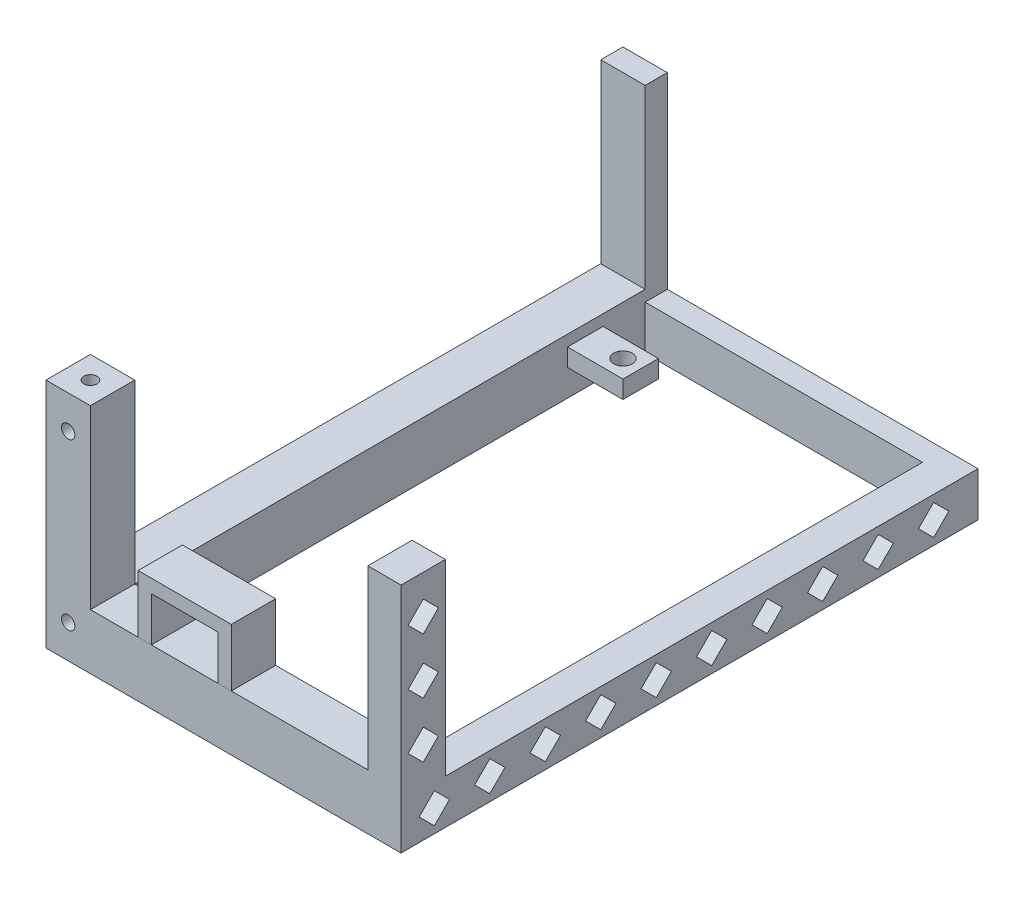
SolidWorks part; units mm, degrees
ref_plane "Front Plane" through (0, 0, 0) normal (0, 0, 1) x (1, 0, 0)
ref_plane "Top Plane" through (0, 0, 0) normal (0, 1, 0) x (1, 0, 0)
ref_plane "Right Plane" through (0, 0, 0) normal (1, 0, 0) x (0, 0, -1)
sketch "Sketch1" plane through (0, 0, 0) normal (0, 1, 0) x (1, 0, 0)
  line L0 (0, 0) -> (-45, 0) construction
  line L1 (35, -65) -> (-45, -65)
  line L2 (35, -65) -> (35, 65)
  line L3 (35, 65) -> (-45, 65)
  line L4 (-45, -65) -> (-45, 65)
  line L5 (0, 0) -> (35, 0) construction
  point P0 (0, 0)
  dimension "D1" = 65
  dimension "D2" = 65
extrude "Boss-Extrude1" add sketch "Sketch1" along normal blind 10
sketch "Sketch2" plane through (0, 10, 0) normal (0, 1, 0) x (1, 0, 0)
  line L0 (35, -65) -> (-45, -65)
  line L1 (-45, -65) -> (-45, 65)
  line L2 (-45, 65) -> (-35, 65)
  line L3 (35, 65) -> (-45, 65) construction
  line L4 (35, -65) -> (35, -55)
  line L5 (35, -65) -> (35, 65) construction
  line L6 (-35, 65) -> (-35, -55)
  line L7 (-35, -55) -> (35, -55)
extrude "Boss-Extrude2" add sketch "Sketch2" along normal blind 42.3
sketch "Sketch3" plane through (35, 0, 0) normal (1, 0, 0) x (0, 0, -1)
  line L1 (20.925, 5) -> (17.5, 8.425)
  line L39 (-55, 10) -> (-65, 10) construction
  line L40 (17.5, 8.425) -> (14.075, 5)
  line L41 (14.075, 5) -> (17.5, 1.575)
  line L42 (17.5, 1.575) -> (20.925, 5)
  line L56 (-65, 52.3) -> (-65, 0) construction
  line L57 (33.425, 5) -> (30, 8.425)
  line L58 (-55, 10) -> (-55, 0) construction
  line L73 (-65, 0) -> (65, 0) construction
  line L74 (30, 8.425) -> (26.575, 5)
  line L75 (-55, 5) -> (65, 5) construction
  line L76 (26.575, 5) -> (30, 1.575)
  line L77 (65, 10) -> (65, 0) construction
  line L118 (5, 8.425) -> (5, 1.575) construction
  line L119 (5, 8.425) -> (1.575, 5)
  line L120 (1.575, 5) -> (5, 1.575)
  line L121 (5, 1.575) -> (8.425, 5)
  line L122 (8.425, 5) -> (5, 8.425)
  line L139 (-4.075, 5) -> (-7.5, 8.425)
  line L140 (-7.5, 8.425) -> (-10.925, 5)
  line L141 (-10.925, 5) -> (-7.5, 1.575)
  line L142 (-7.5, 1.575) -> (-4.075, 5)
  line L143 (-16.575, 5) -> (-20, 8.425)
  line L144 (-20, 8.425) -> (-23.425, 5)
  line L145 (-23.425, 5) -> (-20, 1.575)
  line L146 (-20, 1.575) -> (-16.575, 5)
  line L147 (-29.075, 5) -> (-32.5, 8.425)
  line L148 (-32.5, 8.425) -> (-35.925, 5)
  line L149 (-35.925, 5) -> (-32.5, 1.575)
  line L150 (-32.5, 1.575) -> (-29.075, 5)
  line L151 (-41.575, 5) -> (-45, 8.425)
  line L152 (-45, 8.425) -> (-48.425, 5)
  line L153 (-48.425, 5) -> (-45, 1.575)
  line L154 (-45, 1.575) -> (-41.575, 5)
  line L155 (-54.075, 5) -> (-57.5, 8.425)
  line L156 (-57.5, 8.425) -> (-60.925, 5)
  line L157 (-60.925, 5) -> (-57.5, 1.575)
  line L158 (-57.5, 1.575) -> (-54.075, 5)
  line L159 (-60, 10) -> (-60, 52.3) construction
  line L160 (-65, 52.3) -> (-55, 52.3) construction
  line L161 (-63.425, 31.15) -> (-56.575, 31.15) construction
  line L162 (-63.425, 31.15) -> (-60, 34.575)
  line L163 (-60, 34.575) -> (-56.575, 31.15)
  line L164 (-56.575, 31.15) -> (-60, 27.725)
  line L165 (-60, 27.725) -> (-63.425, 31.15)
  line L166 (-60, 40.225) -> (-63.425, 43.65)
  line L167 (-63.425, 43.65) -> (-60, 47.075)
  line L168 (-60, 47.075) -> (-56.575, 43.65)
  line L169 (-56.575, 43.65) -> (-60, 40.225)
  line L170 (-60, 15.225) -> (-63.425, 18.65)
  line L171 (-63.425, 18.65) -> (-60, 22.075)
  line L172 (-60, 22.075) -> (-56.575, 18.65)
  line L173 (-56.575, 18.65) -> (-60, 15.225)
  line L174 (30, 1.575) -> (33.425, 5)
  line L175 (45.925, 5) -> (42.5, 8.425)
  line L176 (42.5, 8.425) -> (39.075, 5)
  line L177 (39.075, 5) -> (42.5, 1.575)
  line L178 (42.5, 1.575) -> (45.925, 5)
  line L179 (58.425, 5) -> (55, 8.425)
  line L180 (55, 8.425) -> (51.575, 5)
  line L181 (51.575, 5) -> (55, 1.575)
  line L182 (55, 1.575) -> (58.425, 5)
  point P15 (5, 5)
  point P61 (-60, 31.15)
  dimension "D1" = 6
  dimension "D2" = 2
  dimension "D3" = 2
extrude "Cut-Extrude1" cut sketch "Sketch3" against normal blind 5.25
sketch "Sketch4" plane through (0, 10, 0) normal (0, 1, 0) x (1, 0, 0)
  line L0 (-35, 65) -> (-26.5, 65) construction
  line L1 (35, 65) -> (-35, 65) construction
  line L2 (-26.5, 65) -> (-26.5, 46.5) construction
  circle A0 centre (-26.5, 46.5) radius 2.1
  dimension "D1" = 4.2
extrude "Cut-Extrude2" cut sketch "Sketch4" against normal through all
sketch "Sketch5" plane through (0, 10, 0) normal (0, 1, 0) x (1, 0, 0)
  line L0 (-35, -55) -> (-35, 42.5)
  line L1 (27.5, 60) -> (-35, 60)
  line L3 (27.5, 60) -> (27.5, -55)
  line L4 (-35, -55) -> (27.5, -55)
  line L6 (35, -55) -> (35, 65) construction
  line L7 (35, -55) -> (-35, -55) construction
  line L8 (-35, 42.5) -> (-22.5, 42.5)
  line L10 (-35, -55) -> (-35, 65) construction
  line L11 (-35, 60) -> (-35, 50.5)
  line L12 (-35, 50.5) -> (-22.5, 50.5)
  line L13 (-22.5, 50.5) -> (-22.5, 42.5)
  circle A0 centre (-26.5, 46.5) radius 2.1 construction
  dimension "D3" = 4
  dimension "D4" = 4
  dimension "D2" = 4
  dimension "D1" = 7.5
extrude "Cut-Extrude3" cut sketch "Sketch5" against normal through all
sketch "Sketch7" plane through (-35, 0, 0) normal (1, 0, 0) x (0, 0, -1)
  line L0 (-55, 52.3) -> (-55, 12.5)
  line L1 (-55, 52.3) -> (-55, 0) construction
  line L2 (-55, 12.5) -> (60, 12.5)
  line L3 (60, 12.5) -> (60, 52.3)
  line L4 (-55, 52.3) -> (65, 52.3) construction
  line L5 (60, 52.3) -> (-55, 52.3)
  line L6 (65, 52.3) -> (65, 10) construction
  line L7 (42.5, 0) -> (-55, 0) construction
  dimension "D1" = 5
  dimension "D2" = 12.5
extrude "Cut-Extrude4" cut sketch "Sketch7" against normal through all
sketch "Sketch8" plane through (0, 0, 55) normal (0, 0, -1) x (-1, 0, 0)
  line L0 (35, 12.5) -> (35, 52.3)
  line L1 (-35, 52.3) -> (45, 52.3) construction
  line L2 (35, 52.3) -> (-27.5, 52.3)
  line L7 (35, 12.5) -> (-27.5, 12.5)
  line L8 (-27.5, 12.5) -> (-27.5, 52.3)
extrude "Cut-Extrude5" cut sketch "Sketch8" against normal blind 10
sketch "Sketch9" plane through (0, 52.3, 0) normal (0, 1, 0) x (1, 0, 0)
  line L0 (-45, -60) -> (-40, -60) construction
  line L1 (-45, -55) -> (-45, -65) construction
  circle A0 centre (-40, -60) radius 1.5
extrude "Cut-Extrude6" cut sketch "Sketch9" against normal blind 4
sketch "Sketch10" plane through (0, 0, 0) normal (0, -1, 0) x (1, 0, 0)
  circle A0 centre (-40, 60) radius 1.5 construction
  circle A1 centre (-40, 60) radius 1.5
extrude "Cut-Extrude7" cut sketch "Sketch10" against normal blind 4
sketch "Sketch11" plane through (0, 0, 0) normal (0, -1, 0) x (1, 0, 0)
  line L0 (-35, -42.5) -> (-22.5, -42.5)
  line L1 (-22.5, -42.5) -> (-22.5, -50.5)
  line L2 (-22.5, -50.5) -> (-35, -50.5)
  line L3 (-35, -50.5) -> (-35, -42.5)
extrude "Cut-Extrude8" cut sketch "Sketch11" against normal blind 6
sketch "Sketch13" plane through (0, 0, 65) normal (0, 0, 1) x (1, 0, 0)
  line L4 (-21.25, 12.5) -> (-6.25, 12.5)
  line L5 (27.5, 12.5) -> (-35, 12.5) construction
  line L15 (-21.25, 12.5) -> (-21.25, 22.5)
  line L16 (-21.25, 22.5) -> (-6.25, 22.5)
  line L17 (-6.25, 22.5) -> (-6.25, 12.5)
  line L20 (-3.25, 12.5) -> (-3.25, 25.5)
  line L21 (-3.25, 25.5) -> (-24.25, 25.5)
  line L22 (-24.25, 25.5) -> (-24.25, 12.5)
  line L23 (-24.25, 12.5) -> (-21.25, 12.5)
  line L24 (-6.25, 12.5) -> (-3.25, 12.5)
  point P8 (-13.75, 12.5)
  dimension "D1" = 3
  dimension "D2" = 3
  dimension "D3" = 3
extrude "Boss-Extrude3" add sketch "Sketch13" against normal blind 10 separate body
sketch "Sketch14" plane through (0, 0, 65) normal (0, 0, 1) x (1, 0, 0)
  line L0 (-40, 52.3) -> (-40, 44.8) construction
  line L1 (-45, 52.3) -> (-35, 52.3) construction
  line L2 (-40, 0) -> (-40, 7.5) construction
  line L3 (-45, 0) -> (35, 0) construction
  line L4 (-40, 7.5) -> (-45, 7.5) construction
  line L5 (-45, 52.3) -> (-45, 0) construction
  line L6 (-40, 44.8) -> (-45, 44.8) construction
  circle A0 centre (-40, 44.8) radius 1.5
  circle A1 centre (-40, 7.5) radius 1.5
extrude "Cut-Extrude9" cut sketch "Sketch14" against normal blind 4 contours A0 | A1
